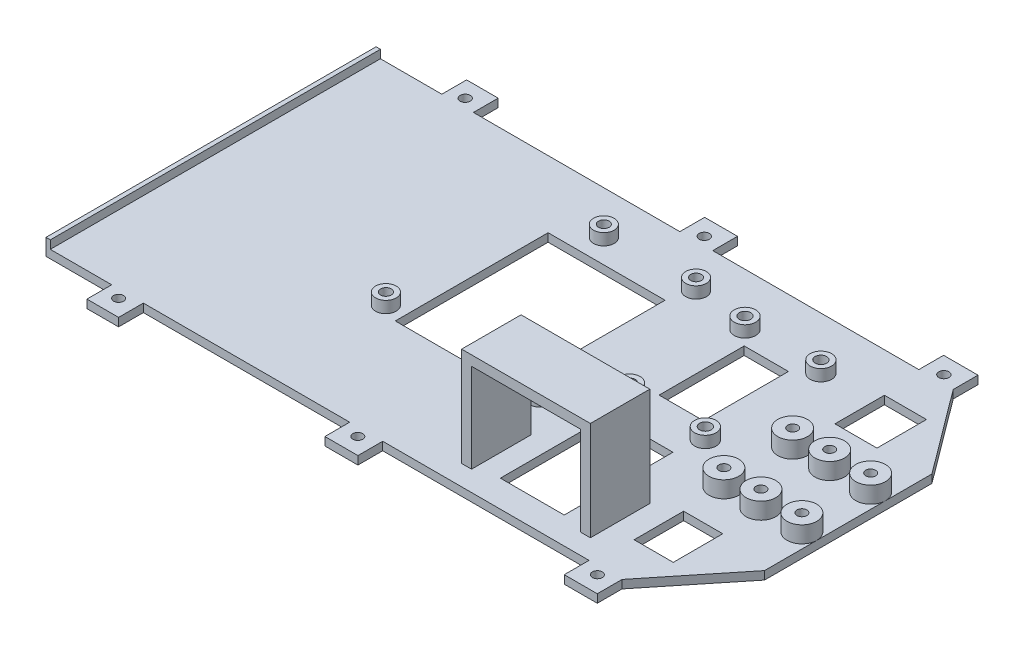
SolidWorks part; units mm, degrees
ref_plane "Front Plane" through (0, 0, 0) normal (0, 0, 1) x (1, 0, 0)
ref_plane "Top Plane" through (0, 0, 0) normal (0, 1, 0) x (1, 0, 0)
ref_plane "Right Plane" through (0, 0, 0) normal (1, 0, 0) x (0, 0, -1)
ref_plane "Plane1" through (0, -17.3323, 0) normal (0, -1, 0) x (-1, 0, 0)
sketch "Sketch2" plane through (0, -17.3323, 0) normal (0, -1, 0) x (-1, 0, 0)
  line L0 (-29.353, -58.531) -> (-29.6746, 41.469) construction
  line L5 (-29.6746, 41.469) -> (-48.6103, 16.0852)
  line L7 (125.2416, 41.469) -> (125.2416, 48.9753)
  line L8 (125.2416, 48.9753) -> (115.6688, 48.9753)
  line L9 (115.6688, 41.469) -> (115.6688, 48.9753)
  line L11 (53.1359, 41.469) -> (53.1359, 48.9753)
  line L12 (53.1359, 48.9753) -> (43.1688, 48.9753)
  line L13 (43.1688, 41.469) -> (43.1688, 48.9753)
  line L15 (-19.2544, 41.469) -> (-19.2544, 48.9753)
  line L16 (-19.2544, 48.9753) -> (-29.6746, 48.9753)
  line L17 (-29.6746, 41.469) -> (-29.6746, 48.9753)
  line L19 (-19.353, -58.531) -> (-19.353, -66.0361)
  line L20 (-19.353, -66.0361) -> (-29.353, -66.0361)
  line L21 (-29.353, -58.531) -> (-29.353, -66.0361)
  line L22 (-29.353, -58.531) -> (-48.6103, -34.6136)
  line L24 (53.147, -58.531) -> (53.147, -66.0361)
  line L25 (53.147, -66.0361) -> (43.147, -66.0361)
  line L26 (43.147, -58.531) -> (43.147, -66.0361)
  line L27 (53.147, -58.531) -> (115.647, -58.531)
  line L29 (125.2416, -58.531) -> (125.2416, -66.0361)
  line L30 (125.2416, -66.0361) -> (115.647, -66.0361)
  line L31 (115.647, -58.531) -> (115.647, -66.0361)
  line L32 (-19.353, -58.531) -> (43.147, -58.531)
  line L33 (-19.2544, 41.469) -> (43.1688, 41.469)
  line L34 (53.1359, 41.469) -> (115.6688, 41.469)
  line L37 (-48.6103, -34.6136) -> (-48.6103, 16.0852)
  line L38 (125.2416, 41.469) -> (145.1434, 41.469)
  line L39 (145.1434, 41.469) -> (145.1434, -58.531)
  line L40 (145.1434, -58.531) -> (125.2416, -58.531)
extrude "Boss-Extrude1" add sketch "Sketch2" against normal blind 2.5
sketch "Sketch24" plane through (0, -14.8323, 0) normal (0, 1, 0) x (1, 0, 0)
  circle A0 centre (-120.6315, 43.9363) radius 1.5346
  circle A1 centre (-48.1932, 43.9363) radius 1.5397
  circle A2 centre (24.3749, 43.9363) radius 1.5351
  circle A3 centre (24.3749, -61.0358) radius 1.5073
  circle A4 centre (-48.1932, -61.0358) radius 1.5018
  circle A5 centre (-120.6315, -61.0358) radius 1.5067
extrude "Cut-Extrude7" cut sketch "Sketch24" against normal through all both and the other way through all
sketch "Sketch28" plane through (0, -14.8323, 0) normal (0, 1, 0) x (1, 0, 0)
  line L0 (48.6103, -34.6136) -> (32.2778, -34.6136) construction
  line L1 (48.6103, 16.0852) -> (32.2778, 16.0852) construction
  line L3 (32.2778, -34.6136) -> (32.2778, 16.0852) construction
  line L4 (37.8914, -34.6136) -> (37.8914, 16.0852) construction
  circle A0 centre (44.0951, -18.794) radius 1.5 construction
  circle A1 centre (44.0951, 2.034) radius 1.5 construction
  circle A2 centre (44.0951, -18.794) radius 1.5
  circle A3 centre (44.0951, 2.034) radius 1.5
  circle A4 centre (44.0951, -18.794) radius 4.5
  circle A5 centre (44.0951, 2.034) radius 4.5
  circle A6 centre (31.6878, 2.034) radius 1.5
  circle A7 centre (31.6878, 2.034) radius 4.5
  circle A8 centre (31.6878, -18.794) radius 4.5
  circle A9 centre (31.6878, -18.794) radius 1.5
  circle A10 centre (20.4604, 2.034) radius 4.5
  circle A11 centre (20.4604, 2.034) radius 1.5
  circle A12 centre (20.4604, -18.794) radius 1.5
  circle A13 centre (20.4604, -18.794) radius 4.5
  dimension "D1" = 3
extrude "Boss-Extrude4" add sketch "Sketch28" along normal blind 5
sketch "Sketch29" plane through (0, -14.8323, 0) normal (0, 1, 0) x (1, 0, 0)
  circle A0 centre (44.0951, -18.794) radius 1.5 construction
  circle A1 centre (44.0951, -18.794) radius 1.5
  circle A2 centre (44.0951, 2.034) radius 1.5 construction
  circle A3 centre (44.0951, 2.034) radius 1.5
  circle A4 centre (20.4604, -18.794) radius 1.5 construction
  circle A5 centre (20.4604, 2.034) radius 1.5 construction
  circle A6 centre (31.6878, 2.034) radius 1.5 construction
  circle A7 centre (31.6878, -18.794) radius 1.5 construction
  circle A8 centre (20.4604, -18.794) radius 1.5
  circle A9 centre (20.4604, 2.034) radius 1.5
  circle A10 centre (31.6878, 2.034) radius 1.5
  circle A11 centre (31.6878, -18.794) radius 1.5
extrude "Cut-Extrude10" cut sketch "Sketch29" against normal through all both and the other way through all
sketch "Sketch30" plane through (0, -14.8323, 0) normal (0, 1, 0) x (1, 0, 0)
  line L0 (-24.3623, -35.4062) -> (-24.3623, -51.4062) construction
  line L1 (-24.3623, -51.4062) -> (12.6377, -51.4062) construction
  line L2 (12.6377, -51.4062) -> (12.6377, -35.4062) construction
  line L3 (12.6377, -35.4062) -> (-24.3623, -35.4062) construction
  line L4 (-24.3623, -35.4062) -> (-24.3623, -51.4062) construction
  line L5 (-24.3623, -51.4062) -> (12.6377, -51.4062) construction
  line L6 (12.6377, -51.4062) -> (12.6377, -35.4062) construction
  line L7 (12.6377, -35.4062) -> (-24.3623, -35.4062) construction
  line L8 (13.6377, -34.4062) -> (-25.3623, -34.4062)
  line L9 (-25.3623, -34.4062) -> (-25.3623, -52.4062)
  line L10 (-25.3623, -52.4062) -> (13.6377, -52.4062)
  line L11 (13.6377, -52.4062) -> (13.6377, -34.4062)
  dimension "D1" = 1
extrude "Boss-Extrude5" add sketch "Sketch30" along normal blind 30
sketch "Sketch31" plane through (0, 0, 34.4062) normal (0, 0, -1) x (-1, 0, 0)
  line L4 (-10.6377, -11.8323) -> (-10.6377, -14.8323)
  line L5 (-13.6377, -14.8323) -> (25.3623, -14.8323) construction
  line L6 (-10.6377, -14.8323) -> (22.3623, -14.8323)
  line L7 (22.3623, -14.8323) -> (22.3623, -11.8323)
  line L8 (-10.6377, -11.8323) -> (22.3623, -11.8323)
  line L9 (22.3623, -11.8323) -> (22.3623, 12.1677)
  line L10 (22.3623, 12.1677) -> (-10.6377, 12.1677)
  line L11 (-10.6377, 12.1677) -> (-10.6377, -11.8323)
  line L13 (22.3623, -11.8323) -> (22.3623, 12.1677)
  line L14 (22.3623, 12.1677) -> (-10.6377, 12.1677)
  line L15 (-10.6377, 12.1677) -> (-10.6377, -11.8323)
  dimension "D1" = 3
extrude "Cut-Extrude11" cut sketch "Sketch31" against normal through all
sketch "Sketch32" plane through (0, -14.8323, 0) normal (0, 1, 0) x (1, 0, 0)
  circle A0 centre (-30.4151, -23.529) radius 1.6192 construction
  circle A1 centre (-78.3322, -22.386) radius 1.6193 construction
  circle A2 centre (-63.0922, 28.4013) radius 1.6193 construction
  circle A3 centre (-35.1649, 28.4013) radius 1.6193 construction
  circle A4 centre (5.365, -9.304) radius 1.75 construction
  circle A5 centre (-17.635, -9.304) radius 1.7551 construction
  circle A6 centre (-17.635, 25.696) radius 1.7551 construction
  circle A7 centre (5.365, 25.696) radius 1.75 construction
  circle A8 centre (-30.4151, -23.529) radius 1.6192
  circle A9 centre (-78.3322, -22.386) radius 1.6193
  circle A10 centre (-63.0922, 28.4013) radius 1.6193
  circle A11 centre (-35.1649, 28.4013) radius 1.6193
  circle A12 centre (5.365, -9.304) radius 1.75
  circle A13 centre (-17.635, -9.304) radius 1.7551
  circle A14 centre (-17.635, 25.696) radius 1.7551
  circle A15 centre (5.365, 25.696) radius 1.75
  circle A16 centre (-78.3322, -22.386) radius 3.1193
  circle A17 centre (-63.0922, 28.4013) radius 3.1193
  circle A18 centre (-35.1649, 28.4013) radius 3.1193
  circle A19 centre (-30.4151, -23.529) radius 3.1193
  circle A20 centre (5.365, 25.696) radius 3.25
  circle A21 centre (5.365, -9.304) radius 3.25
  circle A22 centre (-17.635, -9.304) radius 3.2551
  circle A23 centre (-17.635, 25.696) radius 3.2551
  dimension "D1" = 1.5
extrude "Boss-Extrude6" add sketch "Sketch32" along normal blind 3.5
sketch "Sketch33" plane through (0, -14.8323, 0) normal (0, 1, 0) x (1, 0, 0)
  circle A0 centre (-17.635, 25.696) radius 1.7551 construction
  circle A1 centre (-17.635, -9.304) radius 1.7551 construction
  circle A2 centre (5.365, -9.304) radius 1.75 construction
  circle A3 centre (5.365, 25.696) radius 1.75 construction
  circle A4 centre (-78.3322, -22.386) radius 1.6193 construction
  circle A5 centre (-63.0922, 28.4013) radius 1.6193 construction
  circle A6 centre (-35.1649, 28.4013) radius 1.6193 construction
  circle A7 centre (-30.4151, -23.529) radius 1.6192 construction
  circle A8 centre (-17.635, 25.696) radius 1.7551
  circle A9 centre (-17.635, -9.304) radius 1.7551
  circle A10 centre (5.365, -9.304) radius 1.75
  circle A11 centre (5.365, 25.696) radius 1.75
  circle A12 centre (-78.3322, -22.386) radius 1.6193
  circle A13 centre (-63.0922, 28.4013) radius 1.6193
  circle A14 centre (-35.1649, 28.4013) radius 1.6193
  circle A15 centre (-30.4151, -23.529) radius 1.6192
extrude "Cut-Extrude12" cut sketch "Sketch33" against normal through all both and the other way through all
sketch "Sketch34" plane through (0, -14.8323, 0) normal (0, 1, 0) x (1, 0, 0)
  line L0 (20.7736, -31.294) -> (20.7736, 35.3194) construction
  line L1 (-72.8024, -25.0648) -> (-37.3773, -25.0648)
  line L2 (-72.8024, -25.0648) -> (-72.8024, 21.2295)
  line L3 (-72.8024, 21.2295) -> (-37.3773, 21.2295)
  line L4 (-37.3773, -25.0648) -> (-37.3773, 21.2295)
  line L5 (-13.3947, -4.5608) -> (0, -4.5608)
  line L6 (-13.3947, -4.5608) -> (-13.3947, 21.2295)
  line L7 (-13.3947, 21.2295) -> (0, 21.2295)
  line L8 (0, -4.5608) -> (0, 21.2295)
  line L9 (-15.6494, -17.4545) -> (3.6937, -17.4545)
  line L10 (-15.6494, -17.4545) -> (-15.6494, -50.3918)
  line L11 (-15.6494, -50.3918) -> (3.6937, -50.3918)
  line L12 (3.6937, -17.4545) -> (3.6937, -50.3918)
  line L13 (20.7736, 14.534) -> (33.5059, 14.534)
  line L14 (20.7736, 14.534) -> (20.7736, 29.534)
  line L15 (20.7736, 29.534) -> (33.5059, 29.534)
  line L16 (33.5059, 14.534) -> (33.5059, 29.534)
  line L17 (20.7736, -46.294) -> (32.6293, -46.294)
  line L18 (20.7736, -46.294) -> (20.7736, -31.294)
  line L19 (20.7736, -31.294) -> (32.6293, -31.294)
  line L20 (32.6293, -46.294) -> (32.6293, -31.294)
  circle A0 centre (31.6878, -18.794) radius 4.5 construction
  circle A1 centre (31.6878, 2.034) radius 4.5 construction
  dimension "D1" = 15
  dimension "D2" = 15
  dimension "D3" = 12.5
  dimension "D4" = 12.5
extrude "Cut-Extrude13" cut sketch "Sketch34" against normal through all
sketch "Sketch35" plane through (0, -14.8323, 0) normal (0, 1, 0) x (1, 0, 0)
  line L0 (-145.1434, 41.469) -> (-125.2416, 41.469) construction
  line L1 (-145.1434, -58.531) -> (-143.8349, -58.531)
  line L2 (-145.1434, -58.531) -> (-145.1434, 41.469)
  line L3 (-145.1434, 41.469) -> (-143.8349, 41.469)
  line L4 (-143.8349, -58.531) -> (-143.8349, 41.469)
extrude "Boss-Extrude7" add sketch "Sketch35" along normal blind 2.5
